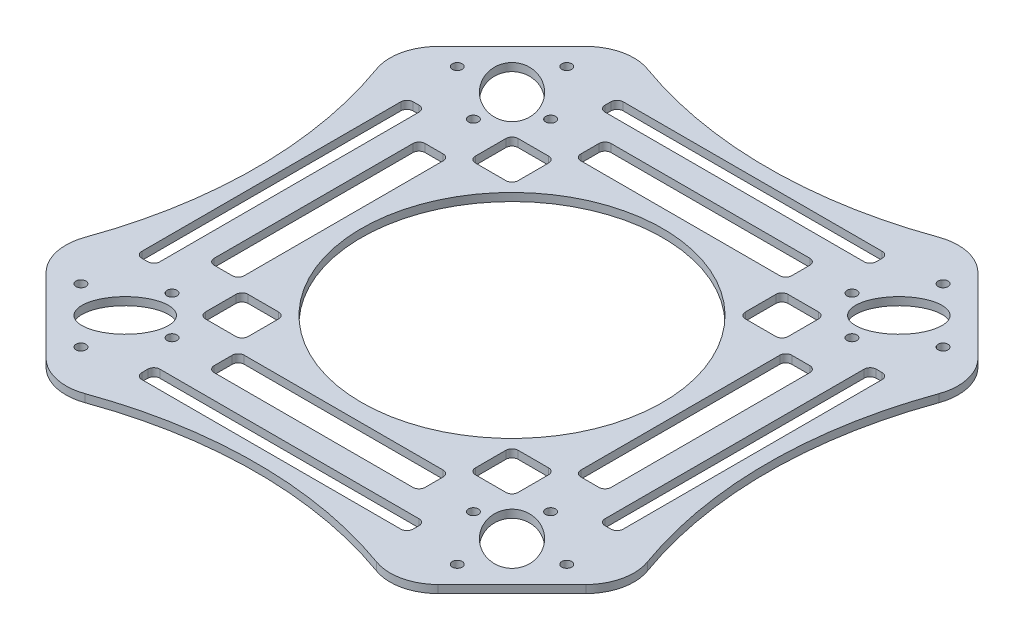
SolidWorks part; units mm, degrees
material "Hexcel AS4C (3000 Filaments)"
ref_plane "Front Plane" through (0, 0, 0) normal (0, 0, 1) x (1, 0, 0)
ref_plane "Top Plane" through (0, 0, 0) normal (0, 1, 0) x (1, 0, 0)
ref_plane "Right Plane" through (0, 0, 0) normal (1, 0, 0) x (0, 0, -1)
sketch "Sketch1" plane through (0, 0, 0) normal (0, 1, 0) x (1, 0, 0)
  line L0 (32.9365, 55.4518) -> (55.4518, 32.9365)
  line L4 (0, 0) -> (0, 83.6325)
  line L5 (0, 0) -> (105.9946, 0)
  line L6 (0, 0) -> (64.2495, 64.2495)
  line L7 (-32.9365, 55.4518) -> (-55.4518, 32.9365)
  line L8 (32.9365, -55.4518) -> (55.4518, -32.9365)
  line L9 (-32.9365, -55.4518) -> (-55.4518, -32.9365)
  arc A1 (55.4518, -32.9365) -> (55.4518, 32.9365) centre (130, 0) cw
  arc A4 (-32.9365, 55.4518) -> (32.9365, 55.4518) centre (0, 130) ccw
  arc A5 (-32.9365, -55.4518) -> (32.9365, -55.4518) centre (0, -130) cw
  arc A6 (-55.4518, -32.9365) -> (-55.4518, 32.9365) centre (-130, 0) ccw
  point P15 (44.1942, 44.1942)
  dimension "D2" = 81.5
  dimension "D1" = 125
  dimension "D3" = 130
extrude "Boss-Extrude1" add sketch "Sketch1" along normal blind 1.5 contours A6 L9 A5 L8 A1 L5 L4 A4 L7 | A4 L4 L6 L0 | L5 A1 L0 L6
scale "Scale1" scale about centroid uniform scaling yes scale factor 2.22222
sketch "Sketch2" plane through (0, 2.4167, 0) normal (0, 1, 0) x (1, 0, 0)
  line L4 (0, 0) -> (159.6132, 0) construction
  line L5 (0, 0) -> (98.2092, 98.2092) construction
  line L6 (73.1923, 123.2261) -> (123.2261, 73.1923) construction
  line L7 (0, 0) -> (0, 107.7777) construction
  line L8 (81.5136, 81.5136) -> (79.3039, 102.3831) construction
  line L9 (81.5136, 81.5136) -> (63.5082, 79.7871) construction
  arc A2 (-73.1923, 123.2261) -> (73.1923, 123.2261) centre (0, 288.8886) ccw construction
  circle A3 centre (63.5082, 79.7871) radius 2.0833
  circle A4 centre (79.3039, 102.3831) radius 2.0833
  circle A5 centre (79.7871, 63.5082) radius 2.0833
  circle A6 centre (102.3831, 79.3039) radius 2.0833
  circle A7 centre (0, 0) radius 63.5
  circle A8 centre (102.3831, -79.3041) radius 2.0833
  circle A9 centre (79.3039, -102.3832) radius 2.0833
  circle A10 centre (63.5082, -79.7872) radius 2.0833
  circle A11 centre (79.7871, -63.5084) radius 2.0833
  circle A12 centre (-79.3041, -102.3832) radius 2.0833
  circle A13 centre (-102.3832, -79.3041) radius 2.0833
  circle A14 centre (-79.7872, -63.5084) radius 2.0833
  circle A15 centre (-63.5084, -79.7872) radius 2.0833
  circle A16 centre (-102.3832, 79.3039) radius 2.0833
  circle A17 centre (-79.3041, 102.3831) radius 2.0833
  circle A18 centre (-63.5084, 79.7871) radius 2.0833
  circle A19 centre (-79.7872, 63.5082) radius 2.0833
  ellipse E0 centre (81.5136, -81.5138) end of major axis (92.3166, -92.3168) minor radius 9.7222
  ellipse E1 centre (81.5136, 81.5136) end of major axis (92.3166, 92.3166) minor radius 9.7222
  ellipse E2 centre (-81.5138, -81.5138) end of major axis (-92.3168, -92.3168) minor radius 9.7222
  ellipse E3 centre (-81.5138, 81.5136) end of major axis (-92.3168, 92.3166) minor radius 9.7222
  point P70 (-0.0001, -0.0001)
  dimension "D16" = 4.1667
  dimension "D17" = 4.1667
  dimension "D2" = 4
  dimension "D3" = 127
  dimension "D8" = 23.6111
  dimension "D9" = 15.2778
  dimension "D10" = 9.7222
  dimension "D11" = 51.044
  dimension "D12" = 39.523
  dimension "D13" = 18.0054
  dimension "D15" = 20.9861
extrude "Cut-Extrude1" cut sketch "Sketch2" against normal through all
fillet "Fillet1" radius 20.32 8 edges at (-123.2261, 0.75, -73.1923) (-73.1923, 0.75, -123.2261) (73.1923, 0.75, -123.2261) (123.2261, 0.75, -73.1923) (123.2261, 0.75, 73.1923) (73.1923, 0.75, 123.2261) (-73.1923, 0.75, 123.2261) (-123.2261, 0.75, 73.1923)
sketch "Sketch3" plane through (0, 2.4167, 0) normal (0, 1, 0) x (1, 0, 0)
  line L0 (0, 0) -> (0, 107.7777) construction
  line L1 (0, 0) -> (98.2092, 98.2092) construction
  line L2 (82.6618, 113.7565) -> (113.7565, 82.6618) construction
  line L3 (83.6477, 44.45) -> (83.6477, -44.45)
  line L4 (-57.15, 93.8077) -> (57.15, 93.8077)
  line L5 (-57.15, 93.8077) -> (-57.15, 101.4277)
  line L6 (-57.15, 101.4277) -> (57.15, 101.4277)
  line L7 (57.15, 93.8077) -> (57.15, 101.4277)
  line L8 (-57.15, 93.8077) -> (57.15, 101.4277) construction
  line L9 (-57.15, 101.4277) -> (57.15, 93.8077) construction
  line L10 (-44.45, 70.9477) -> (44.45, 70.9477)
  line L11 (-44.45, 70.9477) -> (-44.45, 83.6477)
  line L12 (-44.45, 83.6477) -> (44.45, 83.6477)
  line L13 (44.45, 70.9477) -> (44.45, 83.6477)
  line L14 (-44.45, 70.9477) -> (44.45, 83.6477) construction
  line L15 (-44.45, 83.6477) -> (44.45, 70.9477) construction
  line L16 (70.9477, 44.45) -> (83.6477, 44.45)
  line L17 (70.9477, 44.45) -> (70.9477, -44.45)
  line L18 (70.9477, -44.45) -> (83.6477, -44.45)
  line L19 (93.8077, -57.15) -> (101.4277, -57.15)
  line L20 (101.4277, 57.15) -> (101.4277, -57.15)
  line L21 (93.8077, 57.15) -> (93.8077, -57.15)
  line L22 (93.8077, 57.15) -> (101.4277, 57.15)
  line L23 (44.45, -83.6477) -> (-44.45, -83.6477)
  line L24 (44.45, -70.9477) -> (44.45, -83.6477)
  line L25 (44.45, -70.9477) -> (-44.45, -70.9477)
  line L26 (-44.45, -70.9477) -> (-44.45, -83.6477)
  line L27 (-57.15, -93.8077) -> (-57.15, -101.4277)
  line L28 (57.15, -101.4277) -> (-57.15, -101.4277)
  line L29 (57.15, -93.8077) -> (-57.15, -93.8077)
  line L30 (57.15, -93.8077) -> (57.15, -101.4277)
  line L31 (-83.6477, -44.45) -> (-83.6477, 44.45)
  line L32 (-70.9477, -44.45) -> (-83.6477, -44.45)
  line L33 (-70.9477, -44.45) -> (-70.9477, 44.45)
  line L34 (-70.9477, 44.45) -> (-83.6477, 44.45)
  line L35 (-93.8077, 57.15) -> (-101.4277, 57.15)
  line L36 (-101.4277, -57.15) -> (-101.4277, 57.15)
  line L37 (-93.8077, -57.15) -> (-93.8077, 57.15)
  line L38 (-93.8077, -57.15) -> (-101.4277, -57.15)
  arc A0 (-61.4041, 118.5046) -> (61.4041, 118.5046) centre (0, 288.8886) ccw construction
  point P6 (0, 97.6177)
  point P14 (0, 77.2977)
  point P46 (0, 0)
  dimension "D1" = 6.35
  dimension "D2" = 114.3
  dimension "D3" = 7.62
  dimension "D4" = 12.7
  dimension "D5" = 88.9
  dimension "D6" = 10.16
  dimension "D7" = 4
extrude "Cut-Extrude2" cut sketch "Sketch3" against normal through all
fillet "Fillet2" radius 2.54 32 edges at (93.8077, 0.75, -57.15) (101.4277, 0.75, -57.15) (83.6477, 0.75, -44.45) (70.9477, 0.75, -44.45) (101.4277, 0.75, 57.15) (93.8077, 0.75, 57.15) (70.9477, 0.75, 44.45) (83.6477, 0.75, 44.45) (57.15, 0.75, 93.8077) (57.15, 0.75, 101.4277) (44.45, 0.75, 83.6477) (44.45, 0.75, 70.9477) (-44.45, 0.75, 83.6477) (-44.45, 0.75, 70.9477) (-57.15, 0.75, 93.8077) (-57.15, 0.75, 101.4277) (-83.6477, 0.75, 44.45) (-70.9477, 0.75, 44.45) (-93.8077, 0.75, 57.15) (-101.4277, 0.75, 57.15) (-93.8077, 0.75, -57.15) (-101.4277, 0.75, -57.15) (-83.6477, 0.75, -44.45) (-70.9477, 0.75, -44.45) (44.45, 0.75, -70.9477) (-44.45, 0.75, -83.6477) (-44.45, 0.75, -70.9477) (44.45, 0.75, -83.6477) (57.15, 0.75, -93.8077) (57.15, 0.75, -101.4277) (-57.15, 0.75, -93.8077) (-57.15, 0.75, -101.4277)
sketch "Sketch4" plane through (0, 2.4167, 0) normal (0, 1, 0) x (1, 0, 0)
  line L0 (0, 0) -> (0, 107.7777) construction
  line L1 (0, 0) -> (98.2092, 98.2092) construction
  line L2 (82.6618, 113.7565) -> (113.7565, 82.6618) construction
  line L3 (47.9197, -47.9197) -> (65.8803, -47.9197)
  line L4 (47.9197, 47.9197) -> (65.8803, 47.9197)
  line L5 (47.9197, 47.9197) -> (47.9197, 65.8803)
  line L6 (47.9197, 65.8803) -> (65.8803, 65.8803)
  line L7 (65.8803, 47.9197) -> (65.8803, 65.8803)
  line L8 (47.9197, 47.9197) -> (65.8803, 65.8803) construction
  line L9 (47.9197, 65.8803) -> (65.8803, 47.9197) construction
  line L10 (65.8803, -47.9197) -> (65.8803, -65.8803)
  line L11 (47.9197, -65.8803) -> (65.8803, -65.8803)
  line L12 (47.9197, -47.9197) -> (47.9197, -65.8803)
  line L13 (-47.9197, -47.9197) -> (-47.9197, -65.8803)
  line L14 (-47.9197, -65.8803) -> (-65.8803, -65.8803)
  line L15 (-65.8803, -47.9197) -> (-65.8803, -65.8803)
  line L16 (-47.9197, -47.9197) -> (-65.8803, -47.9197)
  line L17 (-47.9197, 47.9197) -> (-65.8803, 47.9197)
  line L18 (-65.8803, 47.9197) -> (-65.8803, 65.8803)
  line L19 (-47.9197, 65.8803) -> (-65.8803, 65.8803)
  line L20 (-47.9197, 47.9197) -> (-47.9197, 65.8803)
  arc A0 (-61.4041, 118.5046) -> (61.4041, 118.5046) centre (0, 288.8886) ccw construction
  point P6 (56.9, 56.9)
  point P29 (0, 0)
  dimension "D1" = 45.72
  dimension "D2" = 25.4
  dimension "D3" = 4
extrude "Cut-Extrude3" cut sketch "Sketch4" against normal through all
fillet "Fillet3" radius 2.54 16 edges at (-65.8803, 0.75, 47.9197) (-65.8803, 0.75, 65.8803) (-47.9197, 0.75, 65.8803) (-47.9197, 0.75, 47.9197) (65.8803, 0.75, 47.9197) (47.9197, 0.75, 65.8803) (65.8803, 0.75, 65.8803) (47.9197, 0.75, 47.9197) (47.9197, 0.75, -65.8803) (65.8803, 0.75, -47.9197) (65.8803, 0.75, -65.8803) (47.9197, 0.75, -47.9197) (-65.8803, 0.75, -47.9197) (-47.9197, 0.75, -47.9197) (-47.9197, 0.75, -65.8803) (-65.8803, 0.75, -65.8803)
